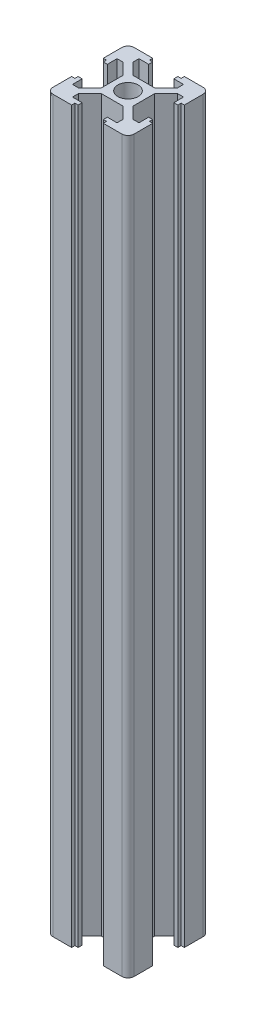
SolidWorks part; units mm, degrees
material "6063-O"
ref_plane "Front Plane" through (0, 0, 0) normal (0, 0, 1) x (1, 0, 0)
ref_plane "Top Plane" through (0, 0, 0) normal (0, 1, 0) x (1, 0, 0)
ref_plane "Right Plane" through (0, 0, 0) normal (1, 0, 0) x (0, 0, -1)
sketch "Sketch1" plane through (0, 0, 0) normal (0, 1, 0) x (1, 0, 0)
  line L0 (0, 14.5399) -> (0, 10) construction
  line L1 (-16.8658, 0) -> (2.5, 0) construction
  line L2 (13.2784, 3.9) -> (3.9, 3.9) construction
  line L3 (0, 0) -> (2.5, 0)
  line L4 (0, 0) -> (0, 2.5)
  line L5 (3.9, 10) -> (8.5, 10)
  line L6 (9.2, 0) -> (16.4291, 0) construction
  line L7 (-2.63, 3.9) -> (2.63, 3.9)
  line L9 (2.5491, 3.9) -> (2.63, 3.9)
  line L10 (3.9, 0) -> (3.9, 2.63)
  line L11 (13.2784, 3.1) -> (2.5491, 3.1) construction
  line L12 (8.2, 7.5573) -> (8.2, -3.0868) construction
  line L13 (9.2, 7.2593) -> (9.2, -8.1534) construction
  line L14 (10, 3.9) -> (9.2, 3.9)
  line L15 (9.2, 3.9) -> (9.2, 3.1)
  line L16 (9.2, 3.1) -> (8.2, 3.1)
  line L17 (8.2, 3.1) -> (8.2, 5.5)
  line L18 (8.2, 5.5) -> (6.77, 5.5)
  line L19 (6.77, 5.5) -> (3.9, 2.63)
  line L20 (5.0973, 5.5) -> (13.0082, 5.5) construction
  line L21 (3.1, 11.2046) -> (3.1, 2.6994) construction
  line L22 (3.9, 10.7498) -> (3.9, 3.9) construction
  line L23 (5.5, 11.523) -> (5.5, 1.4941) construction
  line L24 (-2.2597, 8.2) -> (6.1545, 8.2) construction
  line L25 (-2.9419, 9.2) -> (5.7225, 9.2) construction
  line L26 (3.9, 10) -> (3.9, 9.2)
  line L27 (3.9, 9.2) -> (3.1, 9.2)
  line L28 (3.1, 9.2) -> (3.1, 8.2)
  line L29 (3.1, 8.2) -> (5.5, 8.2)
  line L30 (5.5, 8.2) -> (5.5, 6.77)
  line L31 (5.5, 6.77) -> (2.63, 3.9)
  line L32 (0, 2.5) -> (0, -14.4122) construction
  line L33 (10, 3.9) -> (10, 8.5)
  line L34 (9.2, 0) -> (10, 0)
  line L35 (2.63, 3.9) -> (2.5491, 3.9) construction
  line L36 (3.9, 2.63) -> (3.9, 2.0627) construction
  line L37 (10, -3.9) -> (10, -8.5)
  line L38 (3.9, -10) -> (8.5, -10)
  line L39 (3.9, -10) -> (3.9, -9.2)
  line L40 (3.9, -9.2) -> (3.1, -9.2)
  line L41 (3.1, -9.2) -> (3.1, -8.2)
  line L42 (3.1, -8.2) -> (5.5, -8.2)
  line L43 (5.5, -8.2) -> (5.5, -6.77)
  line L44 (5.5, -6.77) -> (2.63, -3.9)
  line L45 (0, -3.9) -> (2.63, -3.9)
  line L46 (3.9, 0) -> (3.9, -2.63)
  line L47 (6.77, -5.5) -> (3.9, -2.63)
  line L48 (8.2, -5.5) -> (6.77, -5.5)
  line L49 (8.2, -3.1) -> (8.2, -5.5)
  line L50 (9.2, -3.1) -> (8.2, -3.1)
  line L51 (9.2, -3.9) -> (9.2, -3.1)
  line L52 (10, -3.9) -> (9.2, -3.9)
  line L53 (-3.9, -10) -> (-8.5, -10)
  line L54 (-10, -3.9) -> (-10, -8.5)
  line L55 (-10, -3.9) -> (-9.2, -3.9)
  line L56 (-9.2, -3.9) -> (-9.2, -3.1)
  line L57 (-9.2, -3.1) -> (-8.2, -3.1)
  line L58 (-8.2, -3.1) -> (-8.2, -5.5)
  line L59 (-8.2, -5.5) -> (-6.77, -5.5)
  line L60 (-6.77, -5.5) -> (-3.9, -2.63)
  line L61 (-3.9, 0) -> (-3.9, -2.63)
  line L62 (0, -3.9) -> (-2.63, -3.9)
  line L63 (-5.5, -6.77) -> (-2.63, -3.9)
  line L64 (-5.5, -8.2) -> (-5.5, -6.77)
  line L65 (-3.1, -8.2) -> (-5.5, -8.2)
  line L66 (-3.1, -9.2) -> (-3.1, -8.2)
  line L67 (-3.9, -9.2) -> (-3.1, -9.2)
  line L68 (-3.9, -10) -> (-3.9, -9.2)
  line L69 (-10, 3.9) -> (-10, 8.5)
  line L70 (-3.9, 10) -> (-8.5, 10)
  line L71 (-3.9, 10) -> (-3.9, 9.2)
  line L72 (-3.9, 9.2) -> (-3.1, 9.2)
  line L73 (-3.1, 9.2) -> (-3.1, 8.2)
  line L74 (-3.1, 8.2) -> (-5.5, 8.2)
  line L75 (-5.5, 8.2) -> (-5.5, 6.77)
  line L76 (-5.5, 6.77) -> (-2.63, 3.9)
  line L78 (-3.9, 0) -> (-3.9, 2.63)
  line L79 (-6.77, 5.5) -> (-3.9, 2.63)
  line L80 (-8.2, 5.5) -> (-6.77, 5.5)
  line L81 (-8.2, 3.1) -> (-8.2, 5.5)
  line L82 (-9.2, 3.1) -> (-8.2, 3.1)
  line L83 (-9.2, 3.9) -> (-9.2, 3.1)
  line L84 (-10, 3.9) -> (-9.2, 3.9)
  line L85 (0, 3.9) -> (-2.63, 3.9) [skipped]
  circle A0 centre (0, 0) radius 2.5
  arc A1 (8.5, 10) -> (10, 8.5) centre (8.5, 8.5) cw
  arc A2 (10, -8.5) -> (8.5, -10) centre (8.5, -8.5) cw
  arc A4 (-8.5, -10) -> (-10, -8.5) centre (-8.5, -8.5) cw
  arc A6 (-10, 8.5) -> (-8.5, 10) centre (-8.5, 8.5) cw
  point P12 (10, 10)
  point P126 (0, 0)
  dimension "D3" = 5
  dimension "D4" = 1.5
  dimension "D1" = 10
  dimension "D2" = 10
  dimension "D6" = 3.9
  dimension "D7" = 3.9
  dimension "D8" = 3.1
  dimension "D9" = 4
  dimension "D11" = 5.5
  dimension "D12" = 1.8
  dimension "D13" = 0.8
  dimension "D14" = 3.9
  dimension "D15" = 3.1
  dimension "D16" = 5.5
  dimension "D17" = 1.27
  dimension "D18" = 1.27
  dimension "D19" = 1.27
  dimension "D20" = 1.27
extrude "Boss-Extrude1" add sketch "Sketch1" along normal blind 180 contours A6 L69 L84 L83 L82 L81 L80 L79 L78 L61 L60 L59 L58 L57 L56 L55 L54 A4 L53 L68 L67 L66 L65 L64 L63 L62 L45 L44 L43 L42 L41 L40 L39 L38 A2 L37 L52 L51 L50 L49 L48 L47 L46 L10 L19 L18 L17 L16 L15 L14 L33
